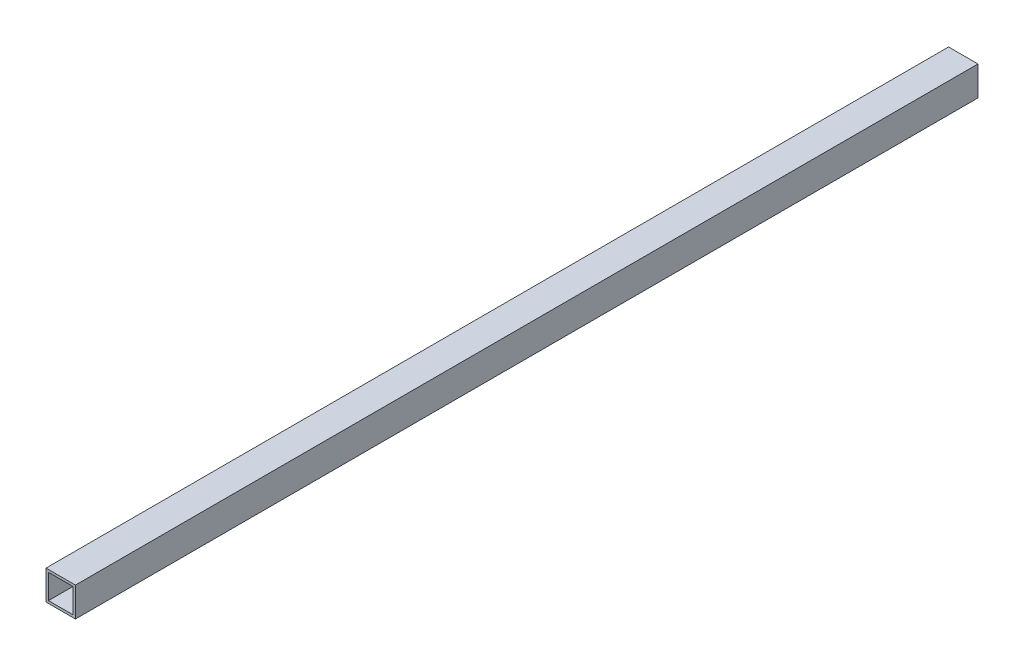
SolidWorks part; units mm, degrees
ref_plane "Front" through (0, 0, 0) normal (0, 0, 1) x (1, 0, 0)
ref_plane "Top" through (0, 0, 0) normal (0, 1, 0) x (1, 0, 0)
ref_plane "Right" through (0, 0, 0) normal (1, 0, 0) x (0, 0, -1)
sketch "Sketch2" plane through (0, 0, 0) normal (0, 0, 1) x (1, 0, 0)
  line L1 (-10.2591, 14.9139) -> (8.7909, 14.9139)
  line L2 (-10.2591, 14.9139) -> (-10.2591, -4.1361)
  line L3 (-10.2591, -4.1361) -> (8.7909, -4.1361)
  line L4 (8.7909, 14.9139) -> (8.7909, -4.1361)
  dimension "D1" = 19.05
  dimension "D2" = 19.05
extrude "Boss-Extrude1" add sketch "Sketch2" along normal blind 584.2 contours L4 L3 L2 L1
sketch "Sketch4" plane through (0, 0, 0) normal (0, 0, -1) x (-1, 0, 0)
  line L8 (8.6716, 13.3264) -> (-7.2034, 13.3264)
  line L9 (-7.2034, 13.3264) -> (-7.2034, -2.5486)
  line L10 (-7.2034, -2.5486) -> (8.6716, -2.5486)
  line L11 (8.6716, -2.5486) -> (8.6716, 13.3264)
  line L12 (8.6716, 13.3264) -> (-7.2034, 13.3264)
  line L13 (-7.2034, 13.3264) -> (-7.2034, -2.5486)
  line L14 (-7.2034, -2.5486) -> (8.6716, -2.5486)
  line L15 (8.6716, -2.5486) -> (8.6716, 13.3264)
  dimension "D1" = 1.5875
extrude "Cut-Extrude1" cut sketch "Sketch4" against normal through all
